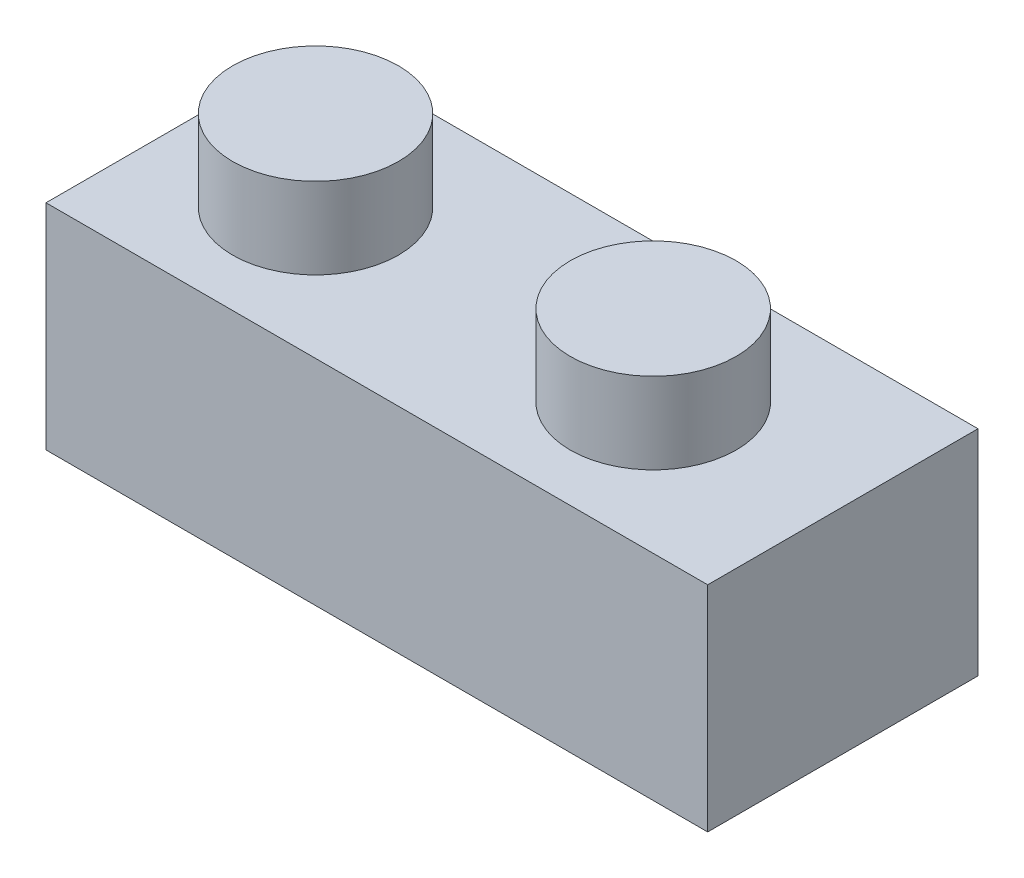
SolidWorks part; units mm, degrees
ref_plane "Plan de face" through (0, 0, 0) normal (0, 0, 1) x (1, 0, 0)
ref_plane "Plan de dessus" through (0, 0, 0) normal (0, 1, 0) x (1, 0, 0)
ref_plane "Plan de droite" through (0, 0, 0) normal (1, 0, 0) x (0, 0, -1)
sketch "Esquisse1" plane through (0, 0, 0) normal (0, 0, 1) x (1, 0, 0)
  line L0 (0, 0) -> (0, 0.0079)
  line L1 (0, 0) -> (0.0245, 0)
  line L2 (0, 0.0079) -> (0.0245, 0.0079)
  line L3 (0.0245, 0) -> (0.0245, 0.0079)
extrude "Boss.-Extru.2" add sketch "Esquisse1" along normal blind 0.01
sketch "Esquisse3" plane through (0, 0, 0) normal (0, -1, 0) x (-1, 0, 0)
  line L0 (-0.0008, -0.0093) -> (-0.0236, -0.0095)
  line L1 (-0.0008, -0.0093) -> (-0.0009, -0.0004)
  line L2 (-0.0236, -0.0095) -> (-0.0237, -0.0006)
  line L3 (-0.0009, -0.0004) -> (-0.0237, -0.0006)
extrude "Enlèv. mat.-Extru.2" cut sketch "Esquisse3" against normal blind 0.007
sketch "Esquisse4" plane through (0, 0.0079, 0) normal (0, 1, 0) x (1, 0, 0)
  circle A0 centre (0.0051, -0.0052) radius 0.0031
  circle A1 centre (0.0176, -0.0052) radius 0.0031
  point P4 (0, 0)
extrude "Boss.-Extru.3" add sketch "Esquisse4" along normal blind 0.003
sketch "Esquisse5" plane through (0, 0.007, 0) normal (0, -1, 0) x (-1, 0, 0)
  circle A0 centre (-0.0117, -0.005) radius 0.0012
  point P2 (-0.0113, -0.0049)
extrude "Boss.-Extru.4" add sketch "Esquisse5" along normal blind 0.0065
